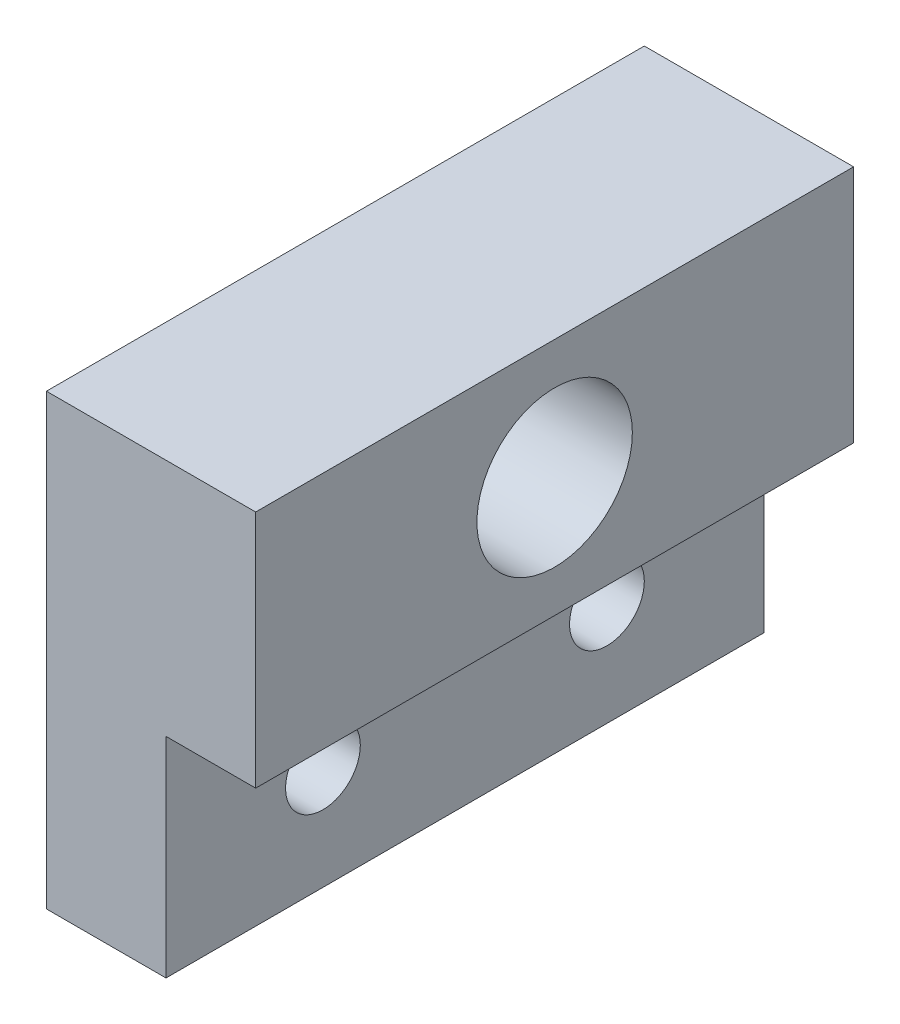
SolidWorks part; units mm, degrees
material "ABS"
ref_plane "Front Plane" through (0, 0, 0) normal (0, 0, 1) x (1, 0, 0)
ref_plane "Top Plane" through (0, 0, 0) normal (0, 1, 0) x (1, 0, 0)
ref_plane "Right Plane" through (0, 0, 0) normal (1, 0, 0) x (0, 0, -1)
sketch "Sketch1" plane through (0, 0, 0) normal (0, 0, 1) x (1, 0, 0)
  line L0 (7, 15) -> (0, 15)
  line L1 (0, 15) -> (0, 0)
  line L2 (0, 0) -> (4, 0)
  line L3 (4, 0) -> (4, 7)
  line L4 (4, 7) -> (7, 7)
  line L5 (7, 7) -> (7, 15)
  dimension "D1" = 3
  dimension "D2" = 7
  dimension "D3" = 8
  dimension "D4" = 15
extrude "Boss-Extrude1" add sketch "Sketch1" along normal blind 20
sketch "Sketch2" plane through (7, 0, 0) normal (1, 0, 0) x (0, 0, -1)
  line L0 (-10, 15) -> (-10, 7) construction
  line L1 (-20, 15) -> (0, 15) construction
  line L2 (-20, 7) -> (0, 7) construction
  circle A0 centre (-10, 11) radius 2.6
  dimension "D1" = 5.2
extrude "Cut-Extrude1" cut sketch "Sketch2" against normal up to next
sketch "Sketch3" plane through (4, 0, 0) normal (1, 0, 0) x (0, 0, -1)
  line L0 (-10, 7) -> (-10, 0) construction
  line L1 (-20, 7) -> (0, 7) construction
  line L2 (-20, 0) -> (0, 0) construction
  circle A0 centre (-14.75, 3.4979) radius 1.25
  circle A1 centre (-5.25, 3.4979) radius 1.25
  dimension "D1" = 2.5
  dimension "D3" = 3.5021
  dimension "D2" = 9.5
extrude "Cut-Extrude2" cut sketch "Sketch3" against normal up to next
